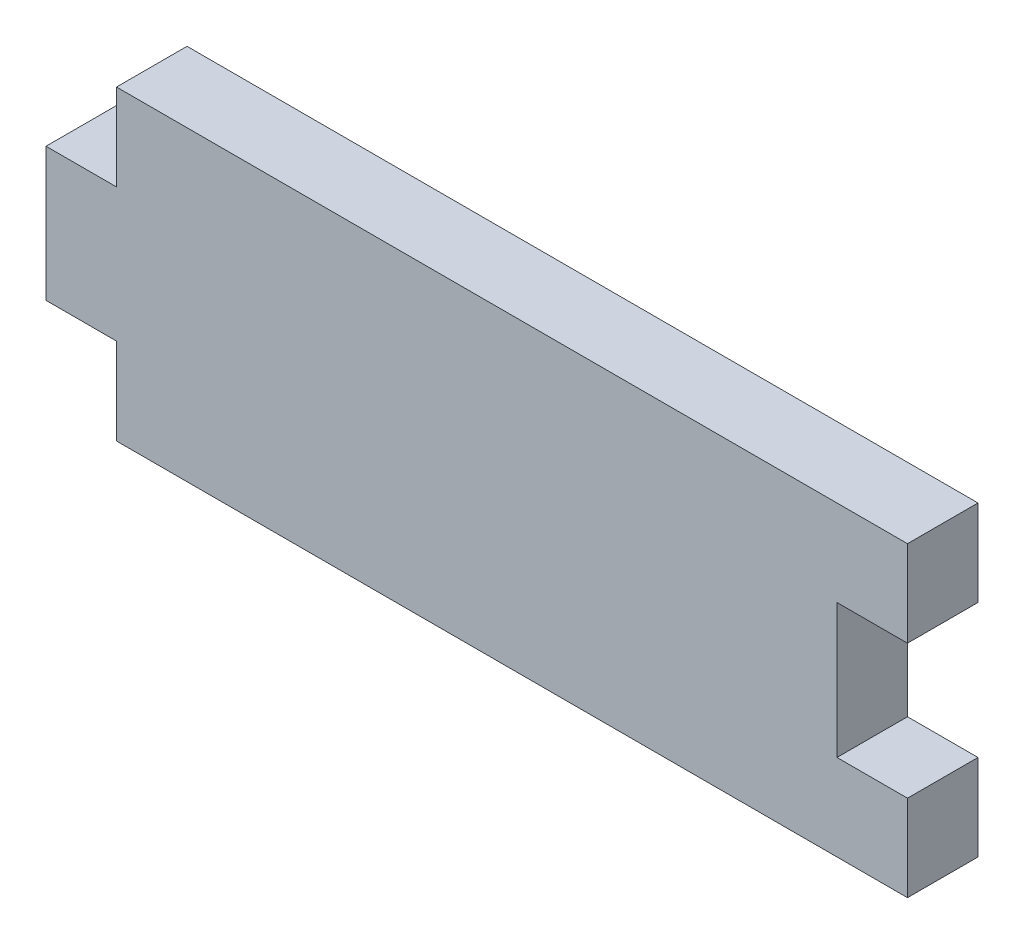
SolidWorks part; units mm, degrees
ref_plane "Front Plane" through (0, 0, 0) normal (0, 0, 1) x (1, 0, 0)
ref_plane "Top Plane" through (0, 0, 0) normal (0, 1, 0) x (1, 0, 0)
ref_plane "Right Plane" through (0, 0, 0) normal (1, 0, 0) x (0, 0, -1)
sketch "Sketch1" plane through (0, 0, 0) normal (0, 0, 1) x (1, 0, 0)
  line L0 (-25.8, -4.3774) -> (-49971.9849, -4.3774) construction
  line L1 (-25.8, -10) -> (25.8, -10)
  line L2 (-25.8, -10) -> (-25.8, -4.3551)
  line L3 (-25.8, 10) -> (25.8, 10)
  line L4 (25.8, -10) -> (25.8, -4.3774)
  line L5 (-25.8, -10) -> (25.8, 10) construction
  line L6 (-25.8, 10) -> (25.8, -10) construction
  line L7 (-25.8, -4.3551) -> (-30.4, -4.3551)
  line L8 (-25.8, 4.3551) -> (-25.8, 10)
  line L9 (-25.8, 4.3551) -> (-30.4, 4.3551)
  line L10 (-30.4, -4.3551) -> (-30.4, 4.3551)
  line L13 (25.8, -4.3774) -> (21.2, -4.3774)
  line L14 (-25.8, 4.3774) -> (-49971.9849, 4.3774) construction
  line L15 (25.8, 4.3774) -> (21.2, 4.3774)
  line L16 (21.2, -4.3774) -> (21.2, 4.3774)
  line L19 (25.8, -4.3774) -> (-11.2936, -4.3774) construction
  line L20 (25.8, 4.3774) -> (-11.2936, 4.3774) construction
  line L21 (25.8, 4.3774) -> (25.8, 10)
  point P0 (0, 0)
  point P6 (-25.8, 0)
  point P11 (25.8, 0)
  point P21 (23.5, -4.3774)
  dimension "D1" = 51.6
  dimension "D2" = 20
  dimension "D3" = 4.6
  dimension "D4" = 4.6
extrude "Boss-Extrude1" add sketch "Sketch1" along normal blind 4.6
equation "\"mat\"=\"mat@levv1.assembly\""
equation "\"D1@Sketch1\"=80-4*\"mat\"-10"
equation "\"D3@Sketch1\" = \"mat\""
equation "\"D4@Sketch1\" = \"mat\""
equation "\"D1@Boss-Extrude1\"=\"mat\""
